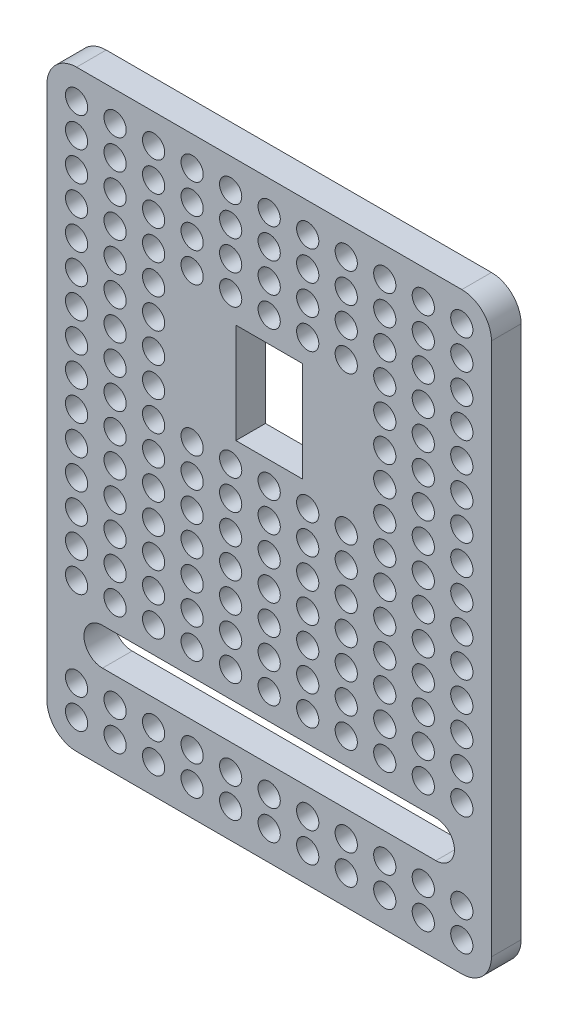
SolidWorks part; units mm, degrees
ref_plane "Спереди" through (0, 0, 0) normal (0, 0, 1) x (1, 0, 0)
ref_plane "Сверху" through (0, 0, 0) normal (0, 1, 0) x (1, 0, 0)
ref_plane "Справа" through (0, 0, 0) normal (1, 0, 0) x (0, 0, -1)
sketch "Эскиз1" plane through (0, 0, 0) normal (0, 0, 1) x (1, 0, 0)
  line L1 (4, 0) -> (56, 0)
  line L2 (0, 4) -> (0, 76)
  line L3 (4, 80) -> (56, 80)
  line L4 (60, 4) -> (60, 76)
  arc A0 (4, 0) -> (0, 4) centre (4, 4) cw
  arc A1 (56, 0) -> (60, 4) centre (56, 4) ccw
  arc A2 (56, 80) -> (60, 76) centre (56, 76) cw
  arc A3 (0, 76) -> (4, 80) centre (4, 76) cw
  point P7 (0, 0)
  point P12 (60, 80)
  point P15 (0, 80)
  dimension "D3" = 4
  dimension "D1" = 80
  dimension "D2" = 60
extrude "Бобышка-Вытянуть1" add sketch "Эскиз1" along normal blind 4 contours L3 A2 L4 A1 L1 A0 L2 A3
sketch "Эскиз2" plane through (0, 0, 4) normal (0, 0, 1) x (1, 0, 0)
  line L0 (30, 80) -> (30, 0) construction
  line L1 (4, 80) -> (56, 80) construction
  line L2 (4, 0) -> (56, 0) construction
  line L3 (7.5, 14) -> (52.5, 14) construction
  line L4 (7.5, 16.5) -> (52.5, 16.5)
  line L5 (7.5, 11.5) -> (52.5, 11.5)
  line L6 (0, 4) -> (0, 76) construction
  arc A0 (7.5, 16.5) -> (7.5, 11.5) centre (7.5, 14) ccw
  arc A1 (52.5, 11.5) -> (52.5, 16.5) centre (52.5, 14) ccw
  point P8 (30, 14)
  dimension "D1" = 11.5
  dimension "D2" = 7.5
extrude "Вырез-Вытянуть1" cut sketch "Эскиз2" against normal blind 4
sketch "Эскиз3" plane through (0, 0, 4) normal (0, 0, 1) x (1, 0, 0)
  line L0 (4, 80) -> (56, 80) construction
  line L1 (0, 4) -> (0, 76) construction
  circle A0 centre (4, 76) radius 1.5
  circle A1 centre (9.2, 76) radius 1.5
  circle A2 centre (14.4, 76) radius 1.5
  circle A3 centre (19.6, 76) radius 1.5
  circle A4 centre (24.8, 76) radius 1.5
  circle A5 centre (30, 76) radius 1.5
  circle A6 centre (35.2, 76) radius 1.5
  circle A7 centre (40.4, 76) radius 1.5
  circle A8 centre (45.6, 76) radius 1.5
  circle A9 centre (50.8, 76) radius 1.5
  circle A10 centre (56, 76) radius 1.5
  circle A11 centre (4, 72) radius 1.5
  circle A12 centre (9.2, 72) radius 1.5
  circle A13 centre (14.4, 72) radius 1.5
  circle A14 centre (19.6, 72) radius 1.5
  circle A15 centre (24.8, 72) radius 1.5
  circle A16 centre (30, 72) radius 1.5
  circle A17 centre (35.2, 72) radius 1.5
  circle A18 centre (40.4, 72) radius 1.5
  circle A19 centre (45.6, 72) radius 1.5
  circle A20 centre (50.8, 72) radius 1.5
  circle A21 centre (56, 72) radius 1.5
  circle A22 centre (4, 68) radius 1.5
  circle A23 centre (9.2, 68) radius 1.5
  circle A24 centre (14.4, 68) radius 1.5
  circle A25 centre (19.6, 68) radius 1.5
  circle A26 centre (24.8, 68) radius 1.5
  circle A27 centre (30, 68) radius 1.5
  circle A28 centre (35.2, 68) radius 1.5
  circle A29 centre (40.4, 68) radius 1.5
  circle A30 centre (45.6, 68) radius 1.5
  circle A31 centre (50.8, 68) radius 1.5
  circle A32 centre (56, 68) radius 1.5
  circle A33 centre (4, 64) radius 1.5
  circle A34 centre (9.2, 64) radius 1.5
  circle A35 centre (14.4, 64) radius 1.5
  circle A36 centre (19.6, 64) radius 1.5
  circle A37 centre (24.8, 64) radius 1.5
  circle A38 centre (30, 64) radius 1.5
  circle A39 centre (35.2, 64) radius 1.5
  circle A40 centre (40.4, 64) radius 1.5
  circle A41 centre (45.6, 64) radius 1.5
  circle A42 centre (50.8, 64) radius 1.5
  circle A43 centre (56, 64) radius 1.5
  circle A44 centre (4, 60) radius 1.5
  circle A45 centre (9.2, 60) radius 1.5
  circle A46 centre (14.4, 60) radius 1.5
  circle A52 centre (45.6, 60) radius 1.5
  circle A53 centre (50.8, 60) radius 1.5
  circle A54 centre (56, 60) radius 1.5
  circle A55 centre (4, 56) radius 1.5
  circle A56 centre (9.2, 56) radius 1.5
  circle A57 centre (14.4, 56) radius 1.5
  circle A63 centre (45.6, 56) radius 1.5
  circle A64 centre (50.8, 56) radius 1.5
  circle A65 centre (56, 56) radius 1.5
  circle A66 centre (4, 52) radius 1.5
  circle A67 centre (9.2, 52) radius 1.5
  circle A68 centre (14.4, 52) radius 1.5
  circle A74 centre (45.6, 52) radius 1.5
  circle A75 centre (50.8, 52) radius 1.5
  circle A76 centre (56, 52) radius 1.5
  circle A77 centre (4, 48) radius 1.5
  circle A78 centre (9.2, 48) radius 1.5
  circle A79 centre (14.4, 48) radius 1.5
  circle A85 centre (45.6, 48) radius 1.5
  circle A86 centre (50.8, 48) radius 1.5
  circle A87 centre (56, 48) radius 1.5
  circle A88 centre (4, 44) radius 1.5
  circle A89 centre (9.2, 44) radius 1.5
  circle A90 centre (14.4, 44) radius 1.5
  circle A91 centre (19.6, 44) radius 1.5
  circle A92 centre (24.8, 44) radius 1.5
  circle A93 centre (30, 44) radius 1.5
  circle A94 centre (35.2, 44) radius 1.5
  circle A95 centre (40.4, 44) radius 1.5
  circle A96 centre (45.6, 44) radius 1.5
  circle A97 centre (50.8, 44) radius 1.5
  circle A98 centre (56, 44) radius 1.5
  circle A99 centre (4, 40) radius 1.5
  circle A100 centre (9.2, 40) radius 1.5
  circle A101 centre (14.4, 40) radius 1.5
  circle A102 centre (19.6, 40) radius 1.5
  circle A103 centre (24.8, 40) radius 1.5
  circle A104 centre (30, 40) radius 1.5
  circle A105 centre (35.2, 40) radius 1.5
  circle A106 centre (40.4, 40) radius 1.5
  circle A107 centre (45.6, 40) radius 1.5
  circle A108 centre (50.8, 40) radius 1.5
  circle A109 centre (56, 40) radius 1.5
  circle A110 centre (4, 36) radius 1.5
  circle A111 centre (9.2, 36) radius 1.5
  circle A112 centre (14.4, 36) radius 1.5
  circle A113 centre (19.6, 36) radius 1.5
  circle A114 centre (24.8, 36) radius 1.5
  circle A115 centre (30, 36) radius 1.5
  circle A116 centre (35.2, 36) radius 1.5
  circle A117 centre (40.4, 36) radius 1.5
  circle A118 centre (45.6, 36) radius 1.5
  circle A119 centre (50.8, 36) radius 1.5
  circle A120 centre (56, 36) radius 1.5
  circle A121 centre (4, 32) radius 1.5
  circle A122 centre (9.2, 32) radius 1.5
  circle A123 centre (14.4, 32) radius 1.5
  circle A124 centre (19.6, 32) radius 1.5
  circle A125 centre (24.8, 32) radius 1.5
  circle A126 centre (30, 32) radius 1.5
  circle A127 centre (35.2, 32) radius 1.5
  circle A128 centre (40.4, 32) radius 1.5
  circle A129 centre (45.6, 32) radius 1.5
  circle A130 centre (50.8, 32) radius 1.5
  circle A131 centre (56, 32) radius 1.5
  circle A132 centre (4, 28) radius 1.5
  circle A133 centre (9.2, 28) radius 1.5
  circle A134 centre (14.4, 28) radius 1.5
  circle A135 centre (19.6, 28) radius 1.5
  circle A136 centre (24.8, 28) radius 1.5
  circle A137 centre (30, 28) radius 1.5
  circle A138 centre (35.2, 28) radius 1.5
  circle A139 centre (40.4, 28) radius 1.5
  circle A140 centre (45.6, 28) radius 1.5
  circle A141 centre (50.8, 28) radius 1.5
  circle A142 centre (56, 28) radius 1.5
  circle A143 centre (4, 24) radius 1.5
  circle A144 centre (9.2, 24) radius 1.5
  circle A145 centre (14.4, 24) radius 1.5
  circle A146 centre (19.6, 24) radius 1.5
  circle A147 centre (24.8, 24) radius 1.5
  circle A148 centre (30, 24) radius 1.5
  circle A149 centre (35.2, 24) radius 1.5
  circle A150 centre (40.4, 24) radius 1.5
  circle A151 centre (45.6, 24) radius 1.5
  circle A152 centre (50.8, 24) radius 1.5
  circle A153 centre (56, 24) radius 1.5
  circle A154 centre (4, 20) radius 1.5
  circle A155 centre (9.2, 20) radius 1.5
  circle A156 centre (14.4, 20) radius 1.5
  circle A157 centre (19.6, 20) radius 1.5
  circle A158 centre (24.8, 20) radius 1.5
  circle A159 centre (30, 20) radius 1.5
  circle A160 centre (35.2, 20) radius 1.5
  circle A161 centre (40.4, 20) radius 1.5
  circle A162 centre (45.6, 20) radius 1.5
  circle A163 centre (50.8, 20) radius 1.5
  circle A164 centre (56, 20) radius 1.5
  circle A187 centre (4, 8) radius 1.5
  circle A188 centre (9.2, 8) radius 1.5
  circle A189 centre (14.4, 8) radius 1.5
  circle A190 centre (19.6, 8) radius 1.5
  circle A191 centre (24.8, 8) radius 1.5
  circle A192 centre (30, 8) radius 1.5
  circle A193 centre (35.2, 8) radius 1.5
  circle A194 centre (40.4, 8) radius 1.5
  circle A195 centre (45.6, 8) radius 1.5
  circle A196 centre (50.8, 8) radius 1.5
  circle A197 centre (56, 8) radius 1.5
  circle A198 centre (4, 4) radius 1.5
  circle A199 centre (9.2, 4) radius 1.5
  circle A200 centre (14.4, 4) radius 1.5
  circle A201 centre (19.6, 4) radius 1.5
  circle A202 centre (24.8, 4) radius 1.5
  circle A203 centre (30, 4) radius 1.5
  circle A204 centre (35.2, 4) radius 1.5
  circle A205 centre (40.4, 4) radius 1.5
  circle A206 centre (45.6, 4) radius 1.5
  circle A207 centre (50.8, 4) radius 1.5
  circle A208 centre (56, 4) radius 1.5
  circle A209 centre (9.2, 16) radius 1.5 [skipped]
  circle A210 centre (14.4, 16) radius 1.5 [skipped]
  circle A211 centre (19.6, 16) radius 1.5 [skipped]
  circle A212 centre (24.8, 16) radius 1.5 [skipped]
  circle A213 centre (30, 16) radius 1.5 [skipped]
  circle A214 centre (35.2, 16) radius 1.5 [skipped]
  circle A215 centre (40.4, 16) radius 1.5 [skipped]
  circle A216 centre (45.6, 16) radius 1.5 [skipped]
  circle A217 centre (50.8, 16) radius 1.5 [skipped]
  circle A218 centre (50.8, 12) radius 1.5 [skipped]
  circle A219 centre (45.6, 12) radius 1.5 [skipped]
  circle A220 centre (40.4, 12) radius 1.5 [skipped]
  circle A221 centre (35.2, 12) radius 1.5 [skipped]
  circle A222 centre (30, 12) radius 1.5 [skipped]
  circle A223 centre (24.8, 12) radius 1.5 [skipped]
  circle A224 centre (19.6, 12) radius 1.5 [skipped]
  circle A225 centre (14.4, 12) radius 1.5 [skipped]
  circle A226 centre (9.2, 12) radius 1.5 [skipped]
  circle A227 centre (4, 12) radius 1.5 [skipped]
  circle A228 centre (4, 16) radius 1.5 [skipped]
  circle A229 centre (56, 16) radius 1.5 [skipped]
  circle A230 centre (56, 12) radius 1.5 [skipped]
  circle A231 centre (19.6, 56) radius 1.5 [skipped]
  circle A232 centre (19.6, 52) radius 1.5 [skipped]
  circle A233 centre (19.6, 48) radius 1.5 [skipped]
  circle A234 centre (24.8, 48) radius 1.5 [skipped]
  circle A235 centre (30, 48) radius 1.5 [skipped]
  circle A236 centre (35.2, 48) radius 1.5 [skipped]
  circle A237 centre (40.4, 48) radius 1.5 [skipped]
  circle A238 centre (40.4, 52) radius 1.5 [skipped]
  circle A239 centre (40.4, 56) radius 1.5 [skipped]
  circle A240 centre (35.2, 60) radius 1.5 [skipped]
  circle A241 centre (30, 60) radius 1.5 [skipped]
  circle A242 centre (24.8, 60) radius 1.5 [skipped]
  circle A243 centre (19.6, 60) radius 1.5 [skipped]
  circle A244 centre (24.8, 56) radius 1.5 [skipped]
  circle A245 centre (30, 56) radius 1.5 [skipped]
  circle A246 centre (30, 52) radius 1.5 [skipped]
  circle A247 centre (35.2, 56) radius 1.5 [skipped]
  circle A248 centre (35.2, 52) radius 1.5 [skipped]
  circle A249 centre (40.4, 60) radius 1.5 [skipped]
  circle A250 centre (24.8, 52) radius 1.5 [skipped]
  dimension "D1" = 3
  dimension "D2" = 4
  dimension "D3" = 4
  dimension "D6" = 5.2
  dimension "D7" = 20
  dimension "D4" = 11
  dimension "D5" = 19
extrude "Вырез-Вытянуть2" cut sketch "Эскиз3" against normal blind 4
sketch "Эскиз5" plane through (0, 0, 4) normal (0, 0, 1) x (1, 0, 0)
  line L0 (0, 4) -> (0, 76) construction
  line L1 (25.5, 60.6) -> (34.5, 60.6)
  line L2 (25.5, 60.6) -> (25.5, 47.1)
  line L3 (25.5, 47.1) -> (34.5, 47.1)
  line L4 (34.5, 60.6) -> (34.5, 47.1)
  line L5 (60, 4) -> (60, 76) construction
  line L6 (4, 80) -> (56, 80) construction
  dimension "D1" = 13.5
  dimension "D2" = 9
  dimension "D3" = 25.5
  dimension "D4" = 25.5
  dimension "D5" = 19.4
extrude "Вырез-Вытянуть6" cut sketch "Эскиз5" against normal blind 17
sketch "Эскиз6" plane through (0, 0, 4) normal (0, 0, 1) x (1, 0, 0)
  line L0 (60, 30.7879) -> (60, 14.7909)
  line L1 (60, 4) -> (60, 76) construction
  circle A0 centre (50.8, 20) radius 1.5 construction
  dimension "D1" = 9.2
